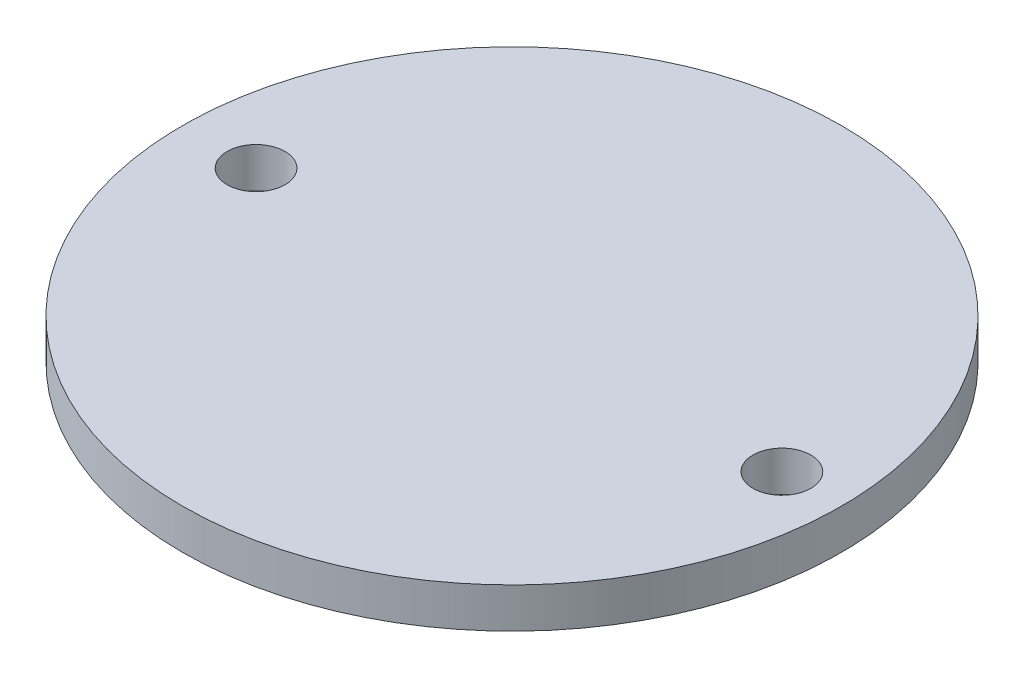
SolidWorks part; units mm, degrees
ref_plane "Front Plane" through (0, 0, 0) normal (0, 0, 1) x (1, 0, 0)
ref_plane "Top Plane" through (0, 0, 0) normal (0, 1, 0) x (1, 0, 0)
ref_plane "Right Plane" through (0, 0, 0) normal (1, 0, 0) x (0, 0, -1)
sketch "Sketch1" plane through (0, 0, 0) normal (0, 1, 0) x (1, 0, 0)
  circle A0 centre (0, 0) radius 12.5349
  dimension "D1" = 25.0698
extrude "Boss-Extrude1" add sketch "Sketch1" along normal mid plane 1.524
sketch "Sketch2" plane through (0, 0.762, 0) normal (0, 1, 0) x (1, 0, 0)
  line L1 (0, 0) -> (24.8872, 0) construction
  line L2 (0, 0) -> (-16.7044, 0) construction
  line L3 (0, 0) -> (0, 16.3078) construction
  line L4 (0, 0) -> (0, -15.84) construction
  circle A0 centre (-9.7349, 0) radius 1.1
  circle A3 centre (10.2651, 0) radius 1.1
  dimension "D1" = 2.2
  dimension "D2" = 2.2
  dimension "D3" = 20
  dimension "D4" = 9.7349
extrude "Cut-Extrude1" cut sketch "Sketch2" against normal through all
